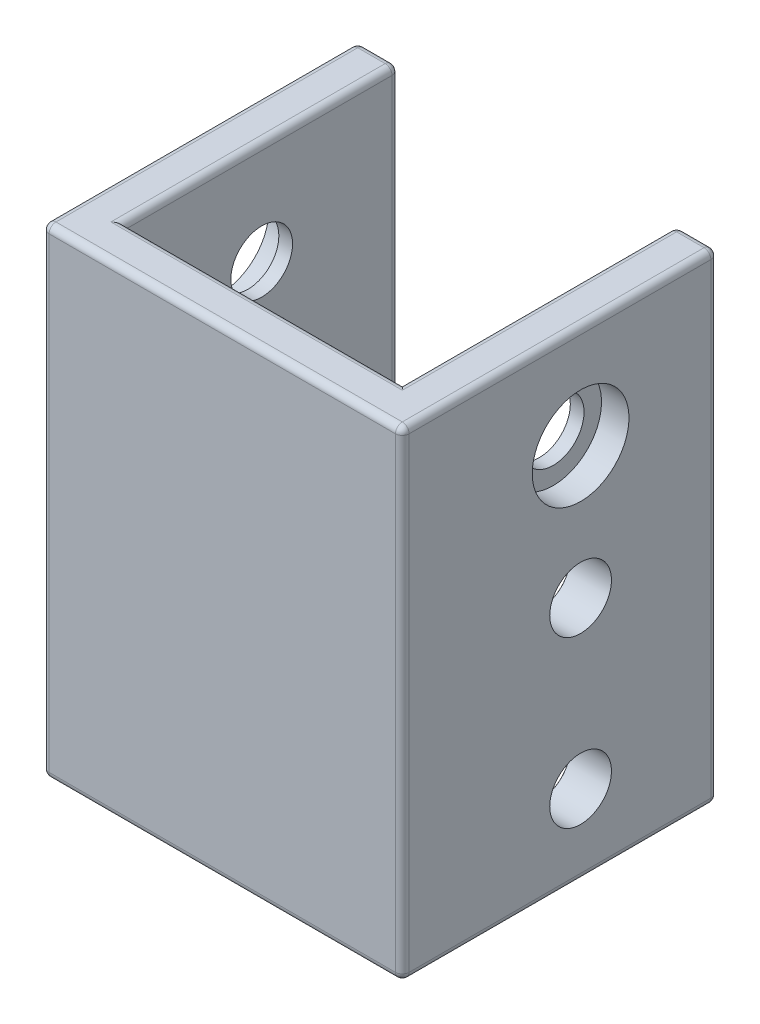
SolidWorks part; units mm, degrees
ref_plane "Front Plane" through (0, 0, 0) normal (0, 0, 1) x (1, 0, 0)
ref_plane "Top Plane" through (0, 0, 0) normal (0, 1, 0) x (1, 0, 0)
ref_plane "Right Plane" through (0, 0, 0) normal (1, 0, 0) x (0, 0, -1)
sketch "Sketch1" plane through (0, 0, 0) normal (0, 1, 0) x (1, 0, 0)
  line L1 (-26.25, -26.25) -> (26.25, -26.25)
  line L2 (-26.25, -26.25) -> (-26.25, 19.75)
  line L4 (26.25, -26.25) -> (26.25, 19.75)
  line L5 (-26.25, -26.25) -> (-20.25, -20.25) construction
  line L6 (20.25, -20.25) -> (26.25, -26.25) construction
  line L11 (-20.25, 19.75) -> (-20.25, -20.25)
  line L12 (-20.25, -20.25) -> (20.25, -20.25)
  line L20 (-20.25, 19.75) -> (-26.25, 19.75)
  line L21 (20.25, 19.75) -> (26.25, 19.75)
  line L22 (20.25, -20.25) -> (20.25, 19.75)
  point P0 (0, 0)
  point P5 (0, 0)
  point P47 (0, 0.8)
  point P49 (0, 0)
  dimension "D1" = 40.5
  dimension "D2" = 6
  dimension "D3" = 6
  dimension "D4" = 46
  dimension "D5" = 6
  dimension "D6" = 46
extrude "Boss-Extrude1" add sketch "Sketch1" along normal blind 70
ref_plane "Plane2" through (20.25, 0, -19.75) normal (1, 0, 0) x (0, 0, -1)
sketch "Sketch8" plane through (26.25, 0, 0) normal (1, 0, 0) x (0, 0, -1)
  line L0 (19.75, 70) -> (19.75, 0) construction
  line L2 (-26.25, 70) -> (19.75, 70) construction
  circle A0 centre (-0.25, 55) radius 4.5
  dimension "D1" = 20
  dimension "D3" = 9
  dimension "D2" = 15
extrude "Cut-Extrude4" cut sketch "Sketch8" against normal through all
sketch "Sketch10" plane through (-26.25, 0, 0) normal (-1, 0, 0) x (0, 0, 1)
  circle A0 centre (0.25, 55) radius 7.05
  dimension "D1" = 14.1
extrude "Cut-Extrude5" cut sketch "Sketch10" against normal blind 4
mirror "Mirror1" about plane through (0, 0, 0) normal (1, 0, 0) of "Cut-Extrude5"
fillet "Fillet13" radius 1 22 edges at (26.25, 0, 3.25) (0, 0, 26.25) (-26.25, 0, 3.25) (-23.25, 0, -19.75) (-26.25, 35, 26.25) (0, 70, 26.25) (-26.25, 70, 3.25) (23.25, 70, -19.75) (-23.25, 70, -19.75) (26.25, 70, 3.25) (26.25, 35, -19.75) (-26.25, 35, -19.75) (26.25, 35, 26.25) (23.25, 0, -19.75) (20.25, 0, 0.25) (-20.25, 0, 0.25) (0, 0, 20.25) (20.25, 70, 0.25) (-20.25, 70, 0.25) (0, 70, 20.25) (-20.25, 35, -19.75) (20.25, 35, -19.75)
sketch "Sketch15" plane through (-26.25, 0, 0) normal (-1, 0, 0) x (0, 0, 1)
  line L0 (-19.75, 1) -> (-19.75, 69) construction
  line L1 (-18.75, 70) -> (25.25, 70) construction
  point P0 (-14.75, 40)
  point P2 (15.25, 40)
  point P4 (15.25, 15)
  point P6 (-14.75, 15)
  dimension "D1" = 5
  dimension "D2" = 35
  dimension "D3" = 25
  dimension "D4" = 30
hole_wizard "M8 Clearance Hole1" positions "Sketch19" profile "Sketch18" hole size "M8" standard "ANSI Metric"
sketch "Sketch19" plane through (-20.25, 0, 0) normal (1, 0, 0) x (0, 0, -1)
  line L0 (19.75, 69) -> (19.75, 1) construction
  point P0 (-0.25, 35.7862)
  point P2 (-0.25, 11.6767)
  dimension "D1" = 20
  dimension "D2" = 20
sketch "Sketch18" plane through (-20.25, 35.7862, 0.25) normal (0, 1, 0) x (0, 0, -1)
  line L0 (0, 0) -> (0, 15.7039)
  line L1 (0, 15.7039) -> (4.5, 13)
  line L2 (4.5, 13) -> (4.5, 0.025)
  line L3 (4.5, 0.025) -> (4.525, 0)
  line L5 (4.525, 0) -> (0, 0)
  line L6 (-4.5, 0.025) -> (-4.525, 0) construction
  line L10 (0, 15.7039) -> (-4.5, 13) construction
  line L11 (0, -6.35) -> (0, 107.95) construction
  dimension "Hole Dia." = 9
  dimension "Hole Depth" = 13
  dimension "Near C'Sink Dia." = 9.05
  dimension "Near C'Sink Angle" = 90
  dimension "Drill Angle" = 118
mirror "Mirror2" about plane through (0, 0, 0) normal (1, 0, 0) of "M8 Clearance Hole1"
ref_plane "Plane3" through (0, 0, 0) normal (1, 0, 0) x (0, 0, -1)
sketch "Sketch20" plane through (0, 0, 0) normal (1, 0, 0) x (0, 0, -1)
  circle A0 centre (-0.25, 55) radius 4.5 construction
  circle A1 centre (-0.25, 55) radius 4.5
